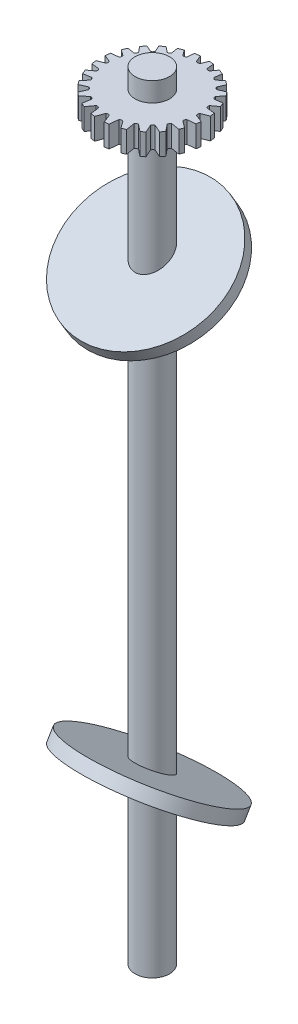
SolidWorks part; units mm, degrees
ref_plane "Alzado" through (0, 0, 0) normal (0, 0, 1) x (1, 0, 0)
ref_plane "Planta" through (0, 0, 0) normal (0, 1, 0) x (1, 0, 0)
ref_plane "Vista lateral" through (0, 0, 0) normal (1, 0, 0) x (0, 0, -1)
sketch "Croquis1" plane through (0, 0, 0) normal (0, 1, 0) x (1, 0, 0)
  circle A0 centre (0, 0) radius 4
  dimension "D1" = 8
extrude "Saliente-Extruir1" add sketch "Croquis1" along normal blind 171
ref_plane "Plano1" through (0, 29.3894, -17.659) normal (0, -0.8572, 0.515) x (-1, 0, 0)
sketch "Croquis2" plane through (0, 29.3894, -17.659) normal (0, -0.8572, 0.515) x (-1, 0, 0)
  circle A0 centre (0, -20.6015) radius 17.5
  dimension "D1" = 35
extrude "Saliente-Extruir2" add sketch "Croquis2" along normal blind 3
sketch "Croquis3" plane through (0, 171, 0) normal (0, 1, 0) x (1, 0, 0)
  line L0 (0, 10.5439) -> (0, 9.4746) construction
  line L1 (1.0507, 12.2165) -> (0.4728, 10.715)
  line L2 (-1.0507, 12.2165) -> (-0.4728, 10.715)
  line L3 (3.9887, 11.5947) -> (3.0142, 10.2559)
  line L4 (2.0886, 12.0824) -> (2.2608, 10.4578)
  line L5 (6.8331, 10.1811) -> (5.5103, 9.1118)
  line L6 (5.0948, 11.153) -> (4.8348, 9.5018)
  line L7 (9.2289, 8.0731) -> (7.6251, 7.3607)
  line L8 (7.7718, 9.484) -> (7.0736, 7.9122)
  line L9 (11.0065, 5.404) -> (9.2147, 5.1219)
  line L10 (9.9409, 7.1781) -> (8.8248, 5.7973)
  line L11 (12.0342, 2.3504) -> (10.1707, 2.5479)
  line L12 (11.4522, 4.381) -> (9.9688, 3.3013)
  line L13 (12.23, -0.8794) -> (10.4279, -0.1858)
  line L14 (12.1952, 1.2744) -> (10.4279, 0.5942)
  line L15 (11.5704, -4.0586) -> (9.9688, -2.8929)
  line L16 (12.1081, -1.9341) -> (10.1707, -2.1395)
  line L17 (10.0948, -6.9601) -> (8.8248, -5.3889)
  line L18 (11.1852, -5.0238) -> (9.2147, -4.7135)
  line L19 (7.9043, -9.3739) -> (7.0736, -7.5038)
  line L20 (9.4803, -7.7763) -> (7.6251, -6.9523)
  line L21 (5.1548, -11.1254) -> (4.8348, -9.0934)
  line L22 (7.1055, -9.9929) -> (5.5103, -8.7034)
  line L23 (2.0445, -12.09) -> (2.2608, -10.0494)
  line L24 (4.2249, -11.5108) -> (3.0142, -9.8475)
  line L25 (-1.2025, -12.2025) -> (-0.4728, -10.3066)
  line L26 (1.0425, -12.2172) -> (0.3071, -10.3066)
  line L27 (-4.3552, -11.4621) -> (-3.1799, -9.8475)
  line L28 (-2.2134, -12.0602) -> (-2.4266, -10.0494)
  line L29 (-7.1933, -9.9299) -> (-5.676, -8.7034)
  line L30 (-5.3091, -11.0526) -> (-5.0005, -9.0934)
  line L31 (-9.5244, -7.7223) -> (-7.7909, -6.9523)
  line L32 (-8.0244, -9.2712) -> (-7.2394, -7.5038)
  line L33 (-11.1961, -4.9994) -> (-9.3805, -4.7135)
  line L34 (-10.1706, -6.8488) -> (-8.9905, -5.3889)
  line L35 (-12.1052, -1.952) -> (-10.3364, -2.1395)
  line L36 (-11.6038, -3.9623) -> (-10.1346, -2.8929)
  line L37 (-12.2015, 1.213) -> (-10.5937, 0.5942)
  line L38 (-12.2343, -0.8172) -> (-10.5937, -0.1858)
  line L39 (-11.488, 4.2864) -> (-10.1346, 3.3013)
  line L40 (-12.0307, 2.3683) -> (-10.3364, 2.5479)
  line L41 (-10.0186, 7.0693) -> (-8.9905, 5.7973)
  line L42 (-11.0184, 5.3798) -> (-9.3805, 5.1219)
  line L43 (-7.8929, 9.3835) -> (-7.2394, 7.9122)
  line L44 (-9.2751, 8.02) -> (-7.7909, 7.3607)
  line L45 (-5.2492, 11.0812) -> (-5.0005, 9.5018)
  line L46 (-6.9233, 10.12) -> (-5.676, 9.1118)
  line L47 (-2.2576, 12.052) -> (-2.4266, 10.4578)
  line L48 (-4.1208, 11.5484) -> (-3.1799, 10.2559)
  arc A0 (-4.1208, 11.5484) -> (-5.2492, 11.0812) centre (0, 0) ccw
  arc A1 (0.4728, 10.715) -> (-0.4728, 10.715) centre (0, 11.2827) cw
  arc A2 (3.0142, 10.2559) -> (2.2608, 10.4578) centre (2.7845, 10.9052) cw
  arc A3 (5.5103, 9.1118) -> (4.8348, 9.5018) centre (5.4564, 9.7985) cw
  arc A4 (7.6251, 7.3607) -> (7.0736, 7.9122) centre (7.7508, 8.0379) cw
  arc A5 (9.2147, 5.1219) -> (8.8248, 5.7973) centre (9.5114, 5.7435) cw
  arc A6 (10.1707, 2.5479) -> (9.9688, 3.3013) centre (10.6182, 3.0715) cw
  arc A7 (10.4279, -0.1858) -> (10.4279, 0.5942) centre (10.9957, 0.2042) cw
  arc A8 (9.9688, -2.8929) -> (10.1707, -2.1395) centre (10.6182, -2.6631) cw
  arc A9 (8.8248, -5.3889) -> (9.2147, -4.7135) centre (9.5114, -5.3351) cw
  arc A10 (7.0736, -7.5038) -> (7.6251, -6.9523) centre (7.7508, -7.6295) cw
  arc A11 (4.8348, -9.0934) -> (5.5103, -8.7034) centre (5.4564, -9.3901) cw
  arc A12 (2.2608, -10.0494) -> (3.0142, -9.8475) centre (2.7845, -10.4968) cw
  arc A13 (-0.4728, -10.3066) -> (0.3071, -10.3066) centre (-0.0829, -10.8743) cw
  arc A14 (-3.1799, -9.8475) -> (-2.4266, -10.0494) centre (-2.9502, -10.4968) cw
  arc A15 (-5.676, -8.7034) -> (-5.0005, -9.0934) centre (-5.6221, -9.3901) cw
  arc A16 (-7.7909, -6.9523) -> (-7.2394, -7.5038) centre (-7.9166, -7.6295) cw
  arc A17 (-9.3805, -4.7135) -> (-8.9905, -5.3889) centre (-9.6772, -5.3351) cw
  arc A18 (-10.3364, -2.1395) -> (-10.1346, -2.8929) centre (-10.7839, -2.6631) cw
  arc A19 (-10.5937, 0.5942) -> (-10.5937, -0.1858) centre (-11.1614, 0.2042) cw
  arc A20 (-10.1346, 3.3013) -> (-10.3364, 2.5479) centre (-10.7839, 3.0715) cw
  arc A21 (-8.9905, 5.7973) -> (-9.3805, 5.1219) centre (-9.6772, 5.7435) cw
  arc A22 (-7.2394, 7.9122) -> (-7.7909, 7.3607) centre (-7.9166, 8.0379) cw
  arc A23 (-5.0005, 9.5018) -> (-5.676, 9.1118) centre (-5.6221, 9.7985) cw
  arc A24 (-2.4266, 10.4578) -> (-3.1799, 10.2559) centre (-2.9502, 10.9052) cw
  arc A25 (-6.9233, 10.12) -> (-7.8929, 9.3835) centre (0, 0) ccw
  arc A26 (-9.2751, 8.02) -> (-10.0186, 7.0693) centre (0, 0) ccw
  arc A27 (-11.0184, 5.3798) -> (-11.488, 4.2864) centre (0, 0) ccw
  arc A28 (-12.0307, 2.3683) -> (-12.2015, 1.213) centre (0, 0) ccw
  arc A29 (-1.0507, 12.2165) -> (-2.2576, 12.052) centre (0, 0) ccw
  arc A30 (2.0886, 12.0824) -> (1.0507, 12.2165) centre (0, 0) ccw
  arc A31 (5.0948, 11.153) -> (3.9887, 11.5947) centre (0, 0) ccw
  arc A32 (7.7718, 9.484) -> (6.8331, 10.1811) centre (0, 0) ccw
  arc A33 (9.9409, 7.1781) -> (9.2289, 8.0731) centre (0, 0) ccw
  arc A34 (11.4522, 4.381) -> (11.0065, 5.404) centre (0, 0) ccw
  arc A35 (12.1952, 1.2744) -> (12.0342, 2.3504) centre (0, 0) ccw
  arc A36 (12.1081, -1.9341) -> (12.23, -0.8794) centre (0, 0) ccw
  arc A37 (11.1852, -5.0238) -> (11.5704, -4.0586) centre (0, 0) ccw
  arc A38 (9.4803, -7.7763) -> (10.0948, -6.9601) centre (0, 0) ccw
  arc A39 (7.1055, -9.9929) -> (7.9043, -9.3739) centre (0, 0) ccw
  arc A40 (4.2249, -11.5108) -> (5.1548, -11.1254) centre (0, 0) ccw
  arc A41 (1.0425, -12.2172) -> (2.0445, -12.09) centre (0, 0) ccw
  arc A42 (-2.2134, -12.0602) -> (-1.2025, -12.2025) centre (0, 0) ccw
  arc A43 (-5.3091, -11.0526) -> (-4.3552, -11.4621) centre (0, 0) ccw
  arc A44 (-8.0244, -9.2712) -> (-7.1933, -9.9299) centre (0, 0) ccw
  arc A45 (-10.1706, -6.8488) -> (-9.5244, -7.7223) centre (0, 0) ccw
  arc A46 (-11.6038, -3.9623) -> (-11.1961, -4.9994) centre (0, 0) ccw
  arc A47 (-12.2343, -0.8172) -> (-12.1052, -1.952) centre (0, 0) ccw
  point P123 (0, 0)
  dimension "D1" = 12.1952
extrude "Saliente-Extruir3" add sketch "Croquis3" along normal blind 5
sketch "Croquis4" plane through (0, 176, 0) normal (0, 1, 0) x (1, 0, 0)
  circle A0 centre (0, 0) radius 4
  dimension "D1" = 8
extrude "Saliente-Extruir4" add sketch "Croquis4" along normal blind 4.5
ref_plane "Plano2" through (0, 102.863, 61.8063) normal (0, 0.8572, 0.515) x (-1, 0, 0)
sketch "Croquis8" plane through (0, 102.863, 61.8063) normal (0, 0.8572, 0.515) x (-1, 0, 0)
  circle A0 centre (0, -72.1053) radius 17.5
  dimension "D1" = 35
extrude "Saliente-Extruir6" add sketch "Croquis8" along normal blind 3
